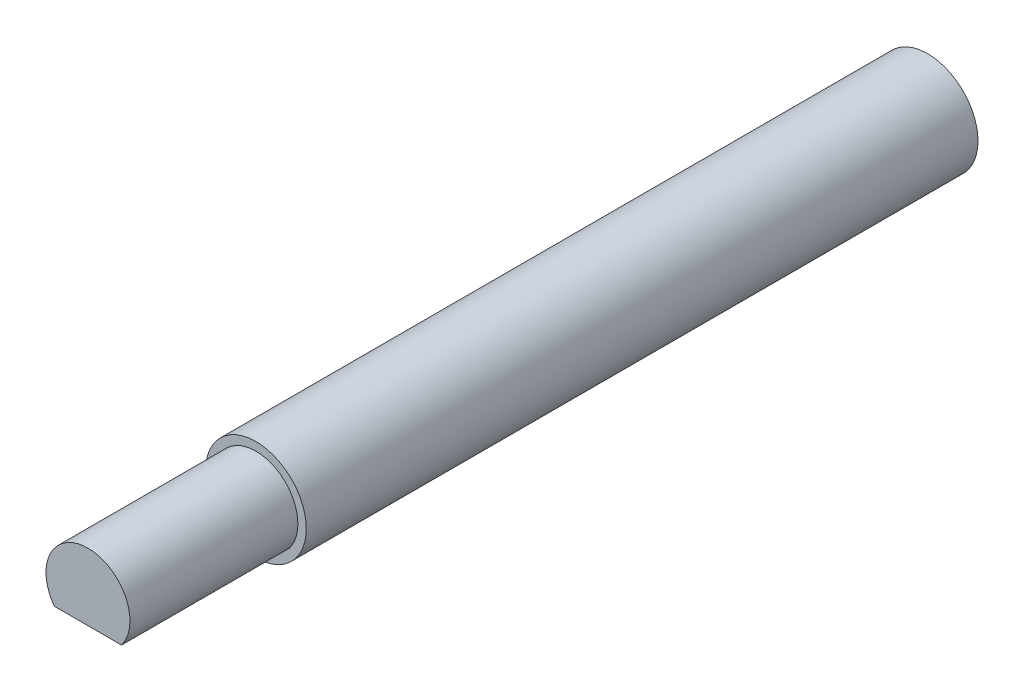
SolidWorks part; units mm, degrees
ref_plane "Front Plane" through (0, 0, 0) normal (0, 0, 1) x (1, 0, 0)
ref_plane "Top Plane" through (0, 0, 0) normal (0, 1, 0) x (1, 0, 0)
ref_plane "Right Plane" through (0, 0, 0) normal (1, 0, 0) x (0, 0, -1)
sketch "Sketch1" plane through (0, 0, 0) normal (0, 0, 1) x (1, 0, 0)
  circle A0 centre (0, 0) radius 6
extrude "Boss-Extrude1" add sketch "Sketch1" along normal blind 80
sketch "Sketch2" plane through (0, 0, 80) normal (0, 0, 1) x (1, 0, 0)
  line L0 (-4, -3) -> (1.6009, -3)
  line L1 (1.6009, -3) -> (4, -3)
  arc A0 (4, -3) -> (-4, -3) centre (0, 0) ccw
  dimension "D1" = 3
extrude "Boss-Extrude2" add sketch "Sketch2" along normal blind 20
